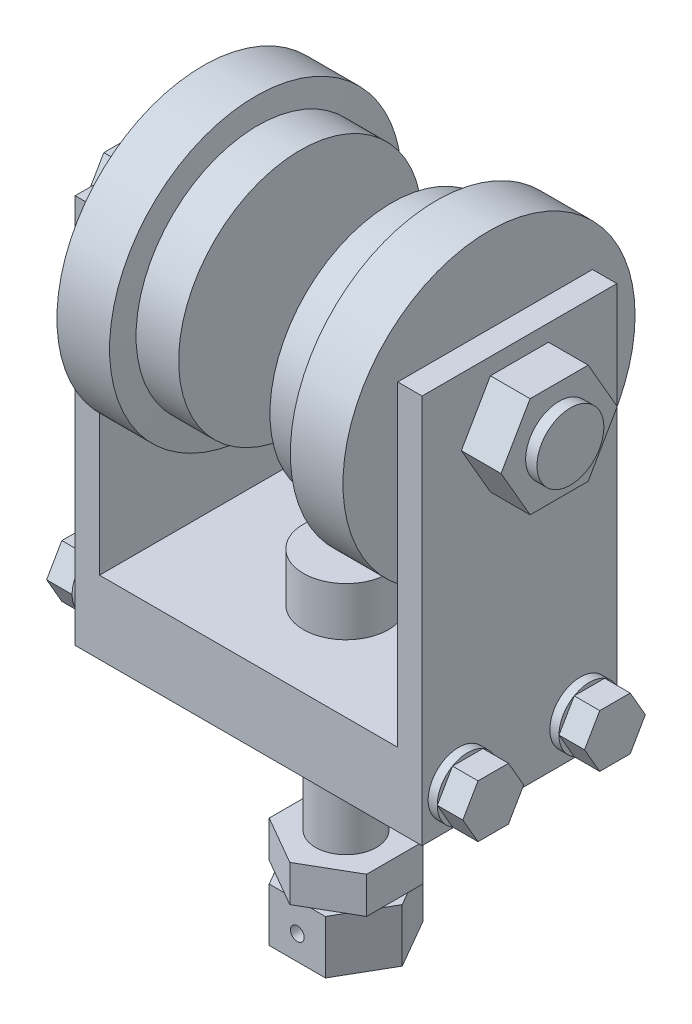
SolidWorks part; units mm, degrees
ref_plane "Front" through (0, 0, 0) normal (0, 0, 1) x (1, 0, 0)
ref_plane "Top" through (0, 0, 0) normal (0, 1, 0) x (1, 0, 0)
ref_plane "Right" through (0, 0, 0) normal (1, 0, 0) x (0, 0, -1)
ref_plane "Z PLANE" through (0, 0, 0) normal (0, 0, 1) x (1, 0, 0)
ref_plane "YOKE BOTTOM" through (0, 0, 0) normal (0, 1, 0) x (-1, 0, 0)
ref_plane "X PLANE" through (0, 0, 0) normal (1, 0, 0) x (0, 0, -1)
sketch "YOKE CROSS SECTION" plane through (0, 0, 0) normal (1, 0, 0) x (0, 0, -1)
  line L0 (0, 0) -> (0, 57.0916) construction
  line L1 (0, 84.8167) -> (0, -84.8167) construction
  line L2 (-50.8, 0) -> (50.8, 0)
  line L3 (69.1602, 0) -> (-69.1602, 0) construction
  line L4 (50.8, 0) -> (50.8, 38.1)
  line L5 (-50.8, 0) -> (-50.8, 38.1)
  line L6 (50.8, 38.1) -> (-50.8, 38.1)
  point P12 (0, 38.1)
  dimension "D1" = 38.1
  dimension "D2" = 101.6
ref_plane "1/2 YOKE LENGTH (A)" through (77.7875, 0, 0) normal (1, 0, 0) x (0, 0, -1)
extrude "YOKE" add sketch "YOKE CROSS SECTION" along normal up to surface (77.7875 mm away) up to plane "1/2 YOKE LENGTH (A)"
sketch "SIDEPLATE PROFILE" plane through (77.7875, 0, 0) normal (1, 0, 0) x (0, 0, -1)
  line L0 (0, 0) -> (0, 74.7424) construction
  line L1 (0, 84.8167) -> (0, -84.8167) construction
  line L2 (-50.8, 0) -> (50.8, 0)
  line L3 (50.8, 0) -> (50.8, 203.2)
  line L4 (-50.8, 0) -> (-50.8, 203.2)
  line L5 (50.8, 203.2) -> (-50.8, 203.2)
  point P11 (0, 203.2)
  dimension "D1" = 203.2
ref_plane "WHEEL HEIGHT" through (0, 168.275, 0) normal (0, 1, 0) x (-1, 0, 0)
ref_plane "SCREW LOCATION X" through (0, 0, 31.75) normal (0, 0, 1) x (1, 0, 0)
ref_plane "SCREW LOCATION Y" through (0, 19.05, 0) normal (0, 1, 0) x (-1, 0, 0)
extrude "SIDEPLATE" add sketch "SIDEPLATE PROFILE" along normal blind 12.7
sketch "WHEEL PIN NUT PROFILE" plane through (90.4875, 0, 0) normal (1, 0, 0) x (0, 0, -1)
  line L0 (0, 84.8167) -> (0, -84.8167) construction
  line L1 (30.3017, 168.275) -> (15.1508, 194.517)
  line L2 (15.1508, 194.517) -> (-15.1508, 194.517)
  line L3 (-15.1508, 194.517) -> (-30.3017, 168.275)
  line L4 (-30.3017, 168.275) -> (-15.1508, 142.033)
  line L5 (-15.1508, 142.033) -> (15.1508, 142.033)
  line L6 (15.1508, 142.033) -> (30.3017, 168.275)
  line L7 (69.1602, 168.275) -> (-69.1602, 168.275) construction
  circle A0 centre (0, 168.275) radius 26.242 construction
  dimension "D1" = 52.484
extrude "WHEEL PIN NUT" add sketch "WHEEL PIN NUT PROFILE" along normal blind 20.7061
sketch "WHEEL PIN PROJECTION PROFILE" plane through (111.1936, 0, 0) normal (1, 0, 0) x (0, 0, -1)
  line L0 (0, 84.8167) -> (0, -84.8167) construction
  line L1 (69.1602, 168.275) -> (-69.1602, 168.275) construction
  circle A0 centre (0, 168.275) radius 17.4625
  dimension "D1" = 34.925
extrude "WHEEL PIN PROJECTION" add sketch "WHEEL PIN PROJECTION PROFILE" along normal blind 5.8826
sketch "LOCKNUTS PROFILE" plane through (90.4875, 0, 0) normal (1, 0, 0) x (0, 0, -1)
  line L0 (-31.75, 84.8167) -> (-31.75, -84.8167) construction
  line L1 (50, 19.05) -> (-50, 19.05) construction
  circle A0 centre (-31.75, 19.05) radius 15.875
  dimension "D1" = 31.75
extrude "LOCKNUTS" add sketch "LOCKNUTS PROFILE" along normal blind 4.7625
sketch "SCREWS PROFILE" plane through (95.25, 0, 0) normal (1, 0, 0) x (0, 0, -1)
  line L0 (50, 19.05) -> (-50, 19.05) construction
  line L1 (-15.8755, 19.05) -> (-23.8127, 32.7978)
  line L2 (-23.8127, 32.7978) -> (-39.6873, 32.7978)
  line L3 (-39.6873, 32.7978) -> (-47.6245, 19.05)
  line L4 (-47.6245, 19.05) -> (-39.6873, 5.3023)
  line L5 (-39.6873, 5.3023) -> (-23.8127, 5.3023)
  line L6 (-23.8127, 5.3023) -> (-15.8755, 19.05)
  line L7 (-31.75, 84.8167) -> (-31.75, -84.8167) construction
  circle A0 centre (-31.75, 19.05) radius 13.7477 construction
  dimension "D1" = 27.4955
extrude "SCREWS" add sketch "SCREWS PROFILE" along normal blind 13.3223
sketch "PROFILE" plane through (0, 38.1, 0) normal (0, 1, 0) x (-1, 0, 0)
  line L0 (84.8167, 0) -> (-84.8167, 0) construction
  line L1 (0, 83.2389) -> (0, -83.2389) construction
  circle A0 centre (0, 0) radius 22.225
  dimension "D1" = 44.45
extrude "KING BOLT HEAD" add sketch "PROFILE" along normal blind 25.4
mirror "Mirror1" about plane through (0, 0, 0) normal (0, 0, 1) of "SCREWS", "LOCKNUTS"
mirror "Mirror5" about plane through (0, 0, 0) normal (1, 0, 0) of bodies 112
ref_plane "TOP OF NUT" through (0, -63.5, 0) normal (0, 1, 0) x (-1, 0, 0)
sketch "DIA." plane through (0, 0, 0) normal (0, -1, 0) x (1, 0, 0)
  line L0 (84.8167, 0) -> (-84.8167, 0) construction
  line L1 (0, -83.2389) -> (0, 83.2389) construction
  circle A0 centre (0, 0) radius 15.875
  dimension "D1" = 31.75
extrude "KING BOLT" add sketch "DIA." along normal up to surface (63.5 mm away) up to plane "TOP OF NUT"
sketch "KING BOLT JAN NUT PROFILE" plane through (0, -63.5, 0) normal (0, -1, 0) x (1, 0, 0)
  line L0 (84.8167, 0) -> (-84.8167, 0) construction
  line L1 (0, -29.3294) -> (25.4, -14.6647)
  line L2 (25.4, -14.6647) -> (25.4, 14.6647)
  line L3 (25.4, 14.6647) -> (0, 29.3294)
  line L4 (0, 29.3294) -> (-25.4, 14.6647)
  line L5 (-25.4, 14.6647) -> (-25.4, -14.6647)
  line L6 (-25.4, -14.6647) -> (0, -29.3294)
  line L7 (0, -83.2389) -> (0, 83.2389) construction
  circle A0 centre (0, 0) radius 25.4 construction
  dimension "D1" = 50.8
extrude "KING BOLT JAM NUT" add sketch "KING BOLT JAN NUT PROFILE" along normal blind 19.0754
sketch "KING BOLT NUT PROFILE" plane through (0, -82.5754, 0) normal (0, -1, 0) x (1, 0, 0)
  line L1 (29.3294, 0) -> (14.6647, 25.4)
  line L2 (14.6647, 25.4) -> (-14.6647, 25.4)
  line L3 (-14.6647, 25.4) -> (-29.3294, 0)
  line L4 (-29.3294, 0) -> (-14.6647, -25.4)
  line L5 (-14.6647, -25.4) -> (14.6647, -25.4)
  line L6 (14.6647, -25.4) -> (29.3294, 0)
  line L10 (0, -83.2389) -> (0, 83.2389) construction
  line L11 (84.8167, 0) -> (-84.8167, 0) construction
  circle A0 centre (0, 0) radius 25.4 construction
  dimension "D1" = 50.8
extrude "KING BOLT NUT" add sketch "KING BOLT NUT PROFILE" along normal blind 27.8003
sketch "Sketch5" plane through (0, -110.3757, 0) normal (0, -1, 0) x (1, 0, 0)
  circle A0 centre (0, 0) radius 15.875 construction
  circle A1 centre (0, 0) radius 15.875
extrude "EXTENDED KING BOLT" add sketch "Sketch5" along normal blind 6.35
chamfer "Chamfer1" distance 2.3812 angle 45 1 edges at (0, -116.7257, -15.875)
ref_plane "MOUNTING REF PLANE" through (0, -34.925, 0) normal (0, 1, 0) x (-1, 0, 0)
sketch "Sketch6" plane through (0, 0, 0) normal (0, 0, 1) x (1, 0, 0)
  line L0 (74.6125, 191.1399) -> (74.6125, 244.475)
  line L1 (46.0375, 231.775) -> (47.1551, 244.475)
  line L2 (77.7875, 168.275) -> (77.7875, 191.1399)
  line L3 (23.8125, 168.275) -> (23.8125, 231.775)
  line L4 (77.7875, 168.275) -> (23.8125, 168.275)
  line L5 (77.7875, 191.1399) -> (74.6125, 191.1399)
  line L6 (23.8125, 231.775) -> (46.0375, 231.775)
  line L8 (74.6125, 244.475) -> (47.1551, 244.475)
  line L9 (69.1602, 168.275) -> (-69.1602, 168.275) construction
  line L11 (77.7875, -75.0522) -> (77.7875, 75.0522) construction
  dimension "D2" = 30.6324
  dimension "D1" = 3.175
  dimension "D3" = 31.75
  dimension "D4" = 53.975
  dimension "D5" = 22.8649
  dimension "D6" = 76.2
  dimension "D7" = 63.5
revolve "WHEEL" add sketch "Sketch6" angle 360 about axis through (117.0762, 168.275, 0) along (-1, 0, 0)
mirror "Mirror6" about plane through (0, 0, 0) normal (1, 0, 0) of "WHEEL"
sketch "Sketch7" plane through (0, 0, 25.4) normal (0, 0, 1) x (1, 0, 0)
  line L0 (0, -83.2389) -> (0, 83.2389) construction
  line L1 (-14.6647, -110.3757) -> (-29.3294, -110.3757) construction
  circle A0 centre (0, -97.6757) radius 3.5719
  dimension "D1" = 7.1437
  dimension "D2" = 12.7
extrude "COTTER PIN HOLE" cut sketch "Sketch7" against normal up to next
sketch "Sketch8" plane through (0, 0, 0) normal (0, -1, 0) x (1, 0, 0)
  circle A0 centre (0, 0) radius 30.1625
  circle A1 centre (0, 0) radius 25.4
  dimension "D1" = 50.8
  dimension "D2" = 60.325
extrude "SPACER" [suppressed] add sketch "Sketch8" along normal blind 12.7
ref_plane "TREAD OF TRACK" through (0, 104.775, 0) normal (0, 1, 0) x (-1, 0, 0)
